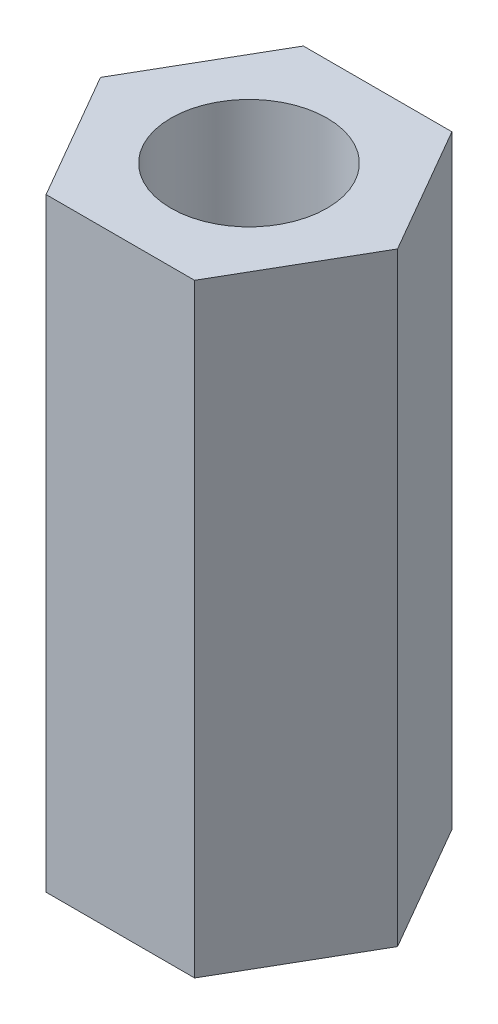
SolidWorks part; units mm, degrees
ref_plane "Front Plane" through (0, 0, 0) normal (0, 0, 1) x (1, 0, 0)
ref_plane "Top Plane" through (0, 0, 0) normal (0, 1, 0) x (1, 0, 0)
ref_plane "Right Plane" through (0, 0, 0) normal (1, 0, 0) x (0, 0, -1)
sketch "Sketch1" plane through (0, 0, 0) normal (0, 1, 0) x (1, 0, 0)
  line L1 (4.5899, 0) -> (2.295, 3.975)
  line L2 (2.295, 3.975) -> (-2.295, 3.975)
  line L3 (-2.295, 3.975) -> (-4.5899, 0)
  line L4 (-4.5899, 0) -> (-2.295, -3.975)
  line L5 (-2.295, -3.975) -> (2.295, -3.975)
  line L6 (2.295, -3.975) -> (4.5899, 0)
  circle A1 centre (0, 0) radius 3.975 construction
  dimension "D2" = 7.95
extrude "Boss-Extrude1" add sketch "Sketch1" along normal blind 18.67
hole_wizard "#10-24 Tapped Hole1" positions "Sketch3" profile "Sketch2" tap size "#10-24" standard "Ansi Inch" end condition through all
sketch "Sketch3" plane through (0, 18.67, 0) normal (0, 1, 0) x (-1, 0, 0)
  point P0 (0, 0)
sketch "Sketch2" plane through (0, 18.67, 0) normal (1, 0, 0) x (0, 0, 1)
  line L0 (0, 0) -> (0, 18.67)
  line L1 (0, 18.67) -> (2.413, 18.67)
  line L2 (2.413, 18.67) -> (2.413, 0)
  line L5 (2.413, 0) -> (0, 0)
  line L11 (0, -6.35) -> (0, 107.95) construction
  dimension "Thread Major Dia." = 4.826
  dimension "Thru Tap Drill Depth" = 18.67
